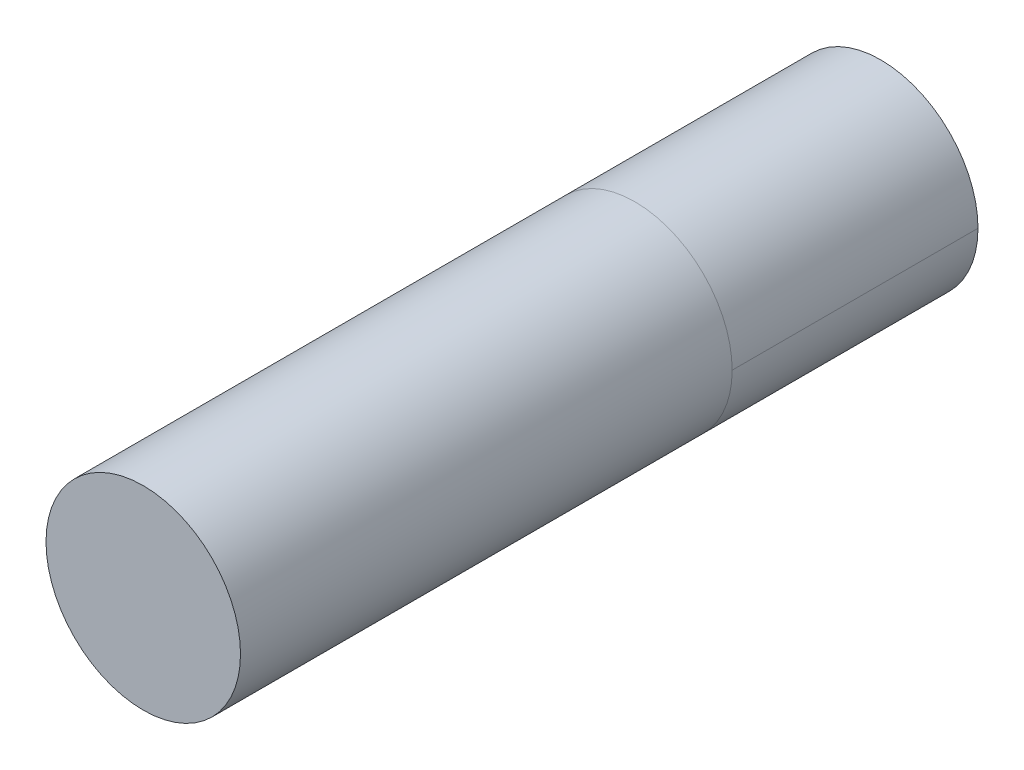
SolidWorks part; units mm, degrees
material "Alloy Steel"
ref_plane "Front Plane" through (0, 0, 0) normal (0, 0, 1) x (1, 0, 0)
ref_plane "Top Plane" through (0, 0, 0) normal (0, 1, 0) x (1, 0, 0)
ref_plane "Right Plane" through (0, 0, 0) normal (1, 0, 0) x (0, 0, -1)
sketch "Sketch1" plane through (0, 0, 0) normal (0, 0, 1) x (1, 0, 0)
  circle A0 centre (0, 0) radius 1.256
  dimension "D1" = 2.5121
extrude "Boss-Extrude1" add sketch "Sketch1" along normal blind 3.175
sketch "Sketch3" plane through (0, 0, 3.175) normal (0, 0, 1) x (1, 0, 0)
  circle A0 centre (0, 0) radius 1.256
  dimension "D1" = 2.5121
extrude "Boss-Extrude2" add sketch "Sketch3" along normal blind 6.35 separate body
split line "Split Line1"
